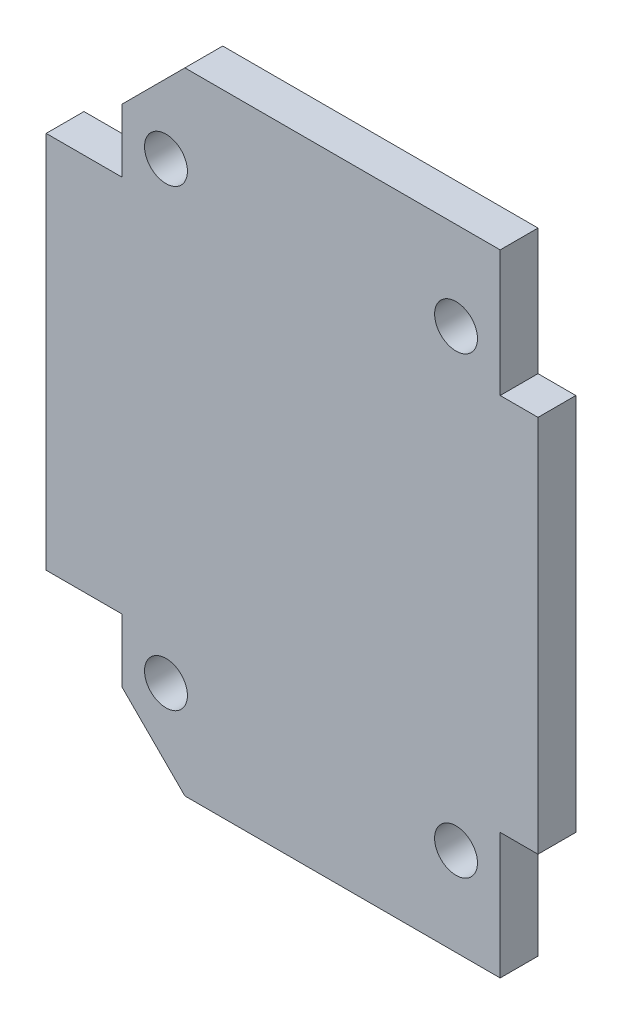
SolidWorks part; units mm, degrees
ref_plane "Front" through (0, 0, 0) normal (0, 0, 1) x (1, 0, 0)
ref_plane "Top" through (0, 0, 0) normal (0, 1, 0) x (1, 0, 0)
ref_plane "Right" through (0, 0, 0) normal (1, 0, 0) x (0, 0, -1)
sketch "Sketch1" plane through (0, 0, 0) normal (0, 0, 1) x (1, 0, 0)
  line L0 (0, 0) -> (0, -7.5117) construction
  line L1 (-15, -25) -> (15, -25)
  line L2 (-15, -25) -> (-15, -15)
  line L3 (-15, 25) -> (15, 25)
  line L4 (15, -25) -> (15, -15)
  line L5 (-11.5, 18) -> (11.5, -18) construction
  line L6 (-11.5, -18) -> (11.5, 18) construction
  line L7 (-15, -25) -> (15, 25) construction
  line L8 (-15, 25) -> (15, -25) construction
  line L9 (-15, -15) -> (-21, -15)
  line L10 (18, -15) -> (18, 15)
  line L11 (-15, 15) -> (-21, 15)
  line L12 (-21, -15) -> (-21, 15)
  line L14 (15, 15) -> (18, 15)
  line L15 (-15, 15) -> (-15, 25)
  line L16 (15, -15) -> (18, -15)
  line L17 (15, 15) -> (15, 25)
  circle A0 centre (11.5, -18) radius 1.7
  circle A1 centre (11.5, 18) radius 1.7
  circle A2 centre (-11.5, 18) radius 1.7
  circle A3 centre (-11.5, -18) radius 1.7
  point P0 (0, 0)
  point P10 (0, 0)
  dimension "D3" = 30
  dimension "D1" = 36
  dimension "D2" = 23
  dimension "D4" = 50
  dimension "D5" = 30
  dimension "D6" = 10
  dimension "D7" = 6
  dimension "D8" = 3
extrude "Boss-Extrude1" add sketch "Sketch1" along normal blind 3
chamfer "Chamfer1" distance 5 angle 45 2 edges at (-15, -25, 1.5) (-15, 25, 1.5)
